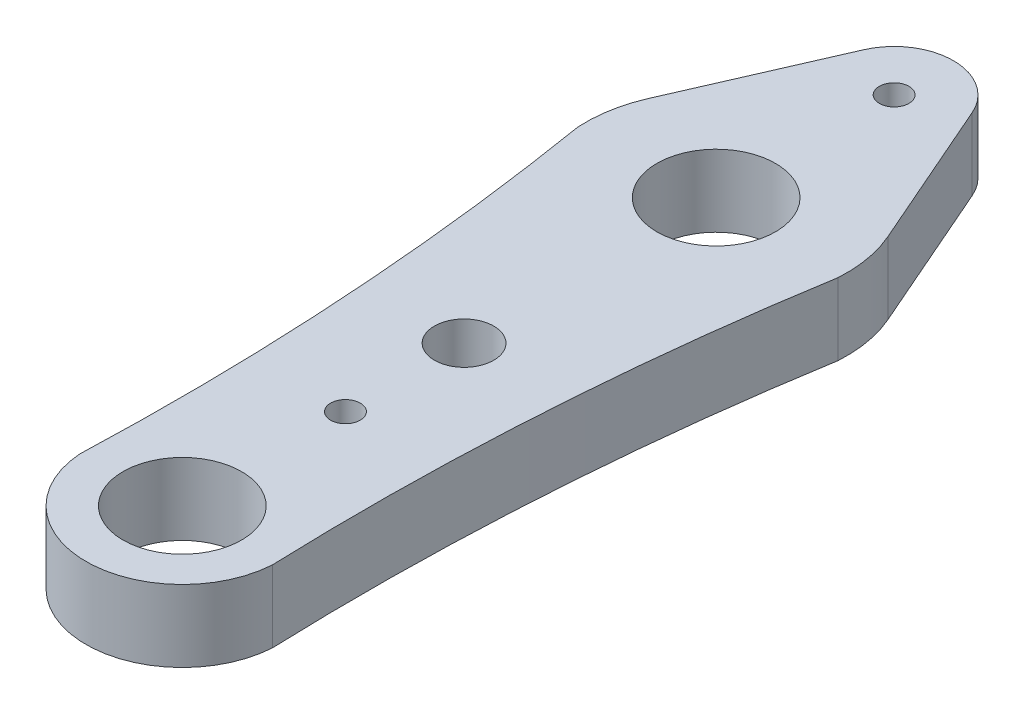
SolidWorks part; units mm, degrees
ref_plane "Front Plane" through (0, 0, 0) normal (0, 0, 1) x (1, 0, 0)
ref_plane "Top Plane" through (0, 0, 0) normal (0, 1, 0) x (1, 0, 0)
ref_plane "Right Plane" through (0, 0, 0) normal (1, 0, 0) x (0, 0, -1)
sketch "Sketch1" plane through (0, 0, 0) normal (0, 1, 0) x (1, 0, 0)
  line L0 (110.4288, 432.0143) -> (849.0954, 432.0143) construction
  line L4 (-8.0653, 20.52) -> (-3.6661, 30.6)
  line L5 (3.6661, 30.6) -> (8.0653, 20.52)
  circle A0 centre (0, 0) radius 2
  circle A1 centre (0, 17) radius 4
  circle A2 centre (0, -19) radius 4
  arc A3 (-6.446, -18.1636) -> (6.446, -18.1636) centre (0, -19) ccw
  arc A4 (8.5164, 14.7841) -> (8.0653, 20.52) centre (0, 17) ccw
  circle A6 centre (0, 29) radius 1
  arc A7 (-8.782, 16.4378) -> (-6.4867, -19.4153) centre (-186.3699, -12.9313) cw
  arc A8 (8.782, 16.4378) -> (6.4867, -19.4153) centre (186.3699, -12.9313) ccw
  arc A9 (-8.0653, 20.52) -> (-8.5164, 14.7841) centre (0, 17) ccw
  arc A10 (3.6661, 30.6) -> (-3.6661, 30.6) centre (0, 29) ccw
  circle A11 centre (0, -8) radius 1
  dimension "D1" = 4
  dimension "D4" = 8
  dimension "D5" = 8
  dimension "D6" = 13
  dimension "D7" = 17.6
  dimension "D9" = 11
  dimension "D10" = 2
  dimension "D11" = 2
  dimension "D2" = 17
  dimension "D3" = 19
  dimension "D8" = 12
extrude "Boss-Extrude1" add sketch "Sketch1" along normal blind 4.85 contours L5 A10 L4 A9 A7 A3 A8 A4 A11 A0 A1 A2 A6
